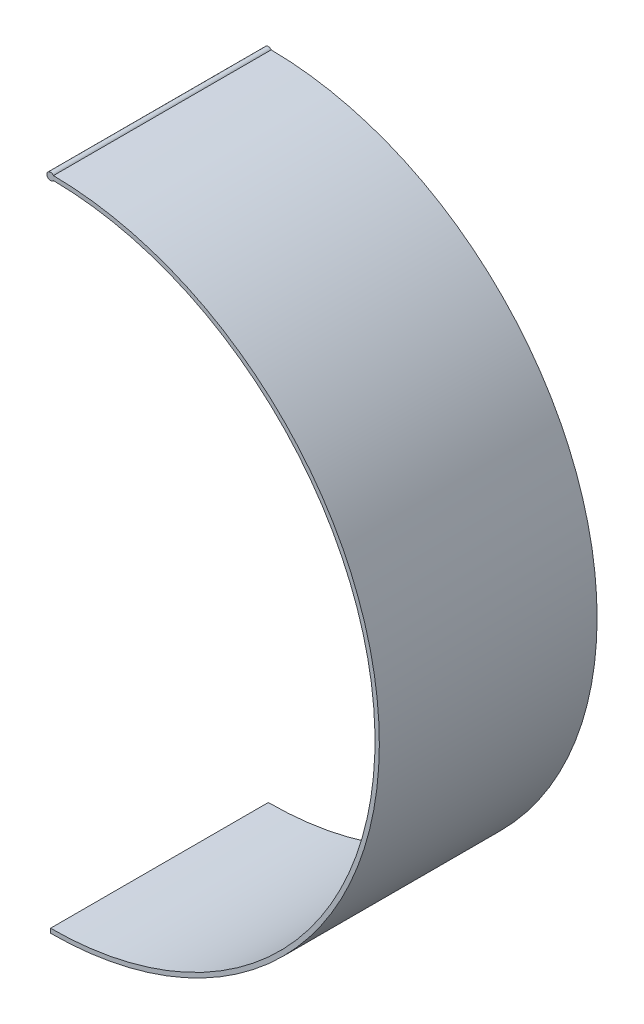
SolidWorks part; units mm, degrees
material "ﾎﾟﾘｴﾁﾚﾝﾃﾚﾌﾀﾗｰﾄ(PET)"
ref_plane "正面" through (0, 0, 0) normal (0, 0, 1) x (1, 0, 0)
ref_plane "平面" through (0, 0, 0) normal (0, 1, 0) x (1, 0, 0)
ref_plane "右側面" through (0, 0, 0) normal (1, 0, 0) x (0, 0, -1)
sketch "ｽｹｯﾁ1" plane through (0, 0, 0) normal (0, 0, 1) x (1, 0, 0)
  circle A0 centre (0, 0) radius 0.25
  dimension "D1" = 0.5
extrude "ﾎﾞｽ - 押し出し1" add sketch "ｽｹｯﾁ1" along normal blind 15
sketch "ｽｹｯﾁ2" plane through (0, 0, 15) normal (0, 0, 1) x (1, 0, 0)
  line L0 (0, -45) -> (0, 0) construction
  line L1 (0, -44.85) -> (0, -45.15)
  line L2 (0, 0.15) -> (0, -0.15)
  arc A0 (0, 0) -> (0, -45) centre (0, -22.5) cw construction
  arc A1 (0, -0.15) -> (0, -44.85) centre (0, -22.5) cw
  arc A2 (0, 0.15) -> (0, -45.15) centre (0, -22.5) cw
  dimension "D2" = 22.5
  dimension "D3" = 0.3
  dimension "D4" = 0.15
  dimension "D1" = 45
extrude "ﾎﾞｽ - 押し出し2" add sketch "ｽｹｯﾁ2" against normal blind 15
sketch3d "3Dｽｹｯﾁ1"
  line L0 (0, 0, 0) -> (0, 0, 10)
  line L1 (0, 0, 0) -> (-10, 0, 0)
  line L2 (0, 0, 0) -> (0, -10, 0)
  dimension "D1" = 10
  dimension "D2" = 10
  dimension "D3" = 10
